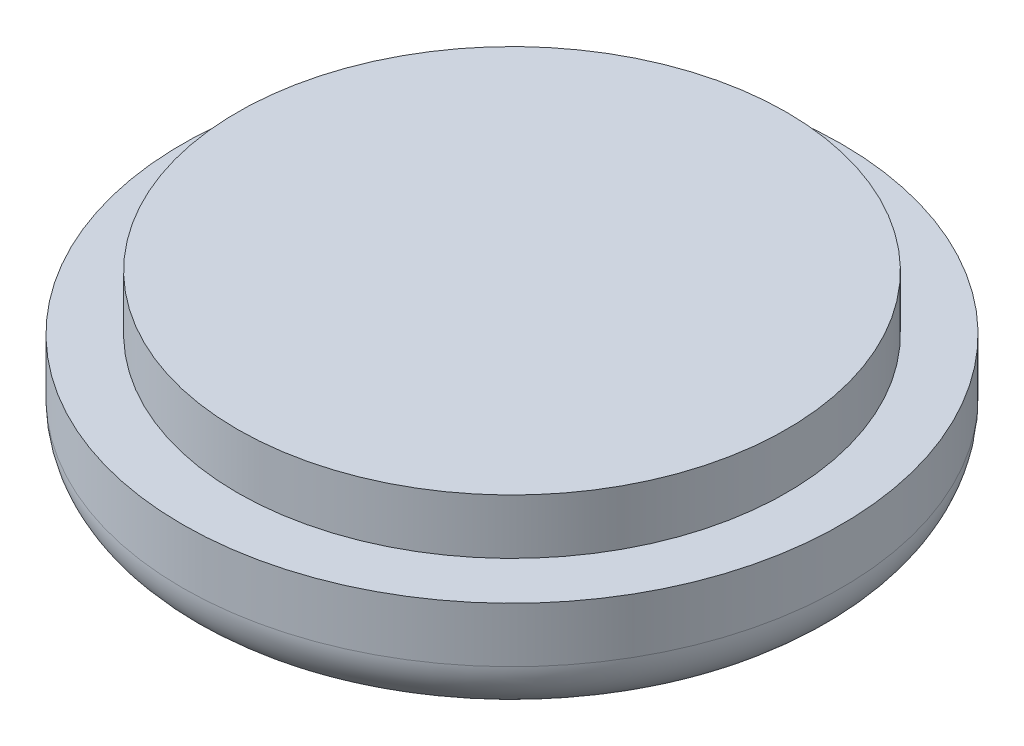
SolidWorks part; units mm, degrees
ref_plane "Front Plane" through (0, 0, 0) normal (0, 0, 1) x (1, 0, 0)
ref_plane "Top Plane" through (0, 0, 0) normal (0, 1, 0) x (1, 0, 0)
ref_plane "Right Plane" through (0, 0, 0) normal (1, 0, 0) x (0, 0, -1)
sketch "Sketch1" plane through (0, 0, 0) normal (0, 1, 0) x (1, 0, 0)
  circle A0 centre (0, 0) radius 60
extrude "Boss-Extrude1" add sketch "Sketch1" along normal blind 20
sketch "Sketch2" plane through (0, 20, 0) normal (0, 1, 0) x (1, 0, 0)
  circle A0 centre (0, 0) radius 50
extrude "Boss-Extrude2" add sketch "Sketch2" along normal blind 10
fillet "Fillet1" radius 10 1 edges at (0, 0, 60)
